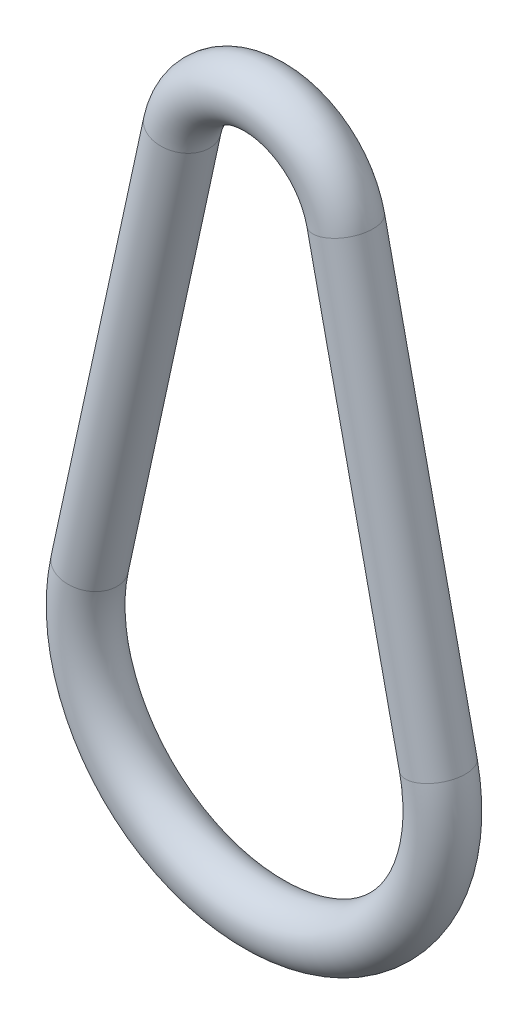
SolidWorks part; units mm, degrees
ref_plane "Front Plane" through (0, 0, 0) normal (0, 0, 1) x (1, 0, 0)
ref_plane "Top Plane" through (0, 0, 0) normal (0, 1, 0) x (1, 0, 0)
ref_plane "Right Plane" through (0, 0, 0) normal (1, 0, 0) x (0, 0, -1)
sketch "Sketch1" plane through (0, 0, 0) normal (0, 0, 1) x (1, 0, 0)
  line L0 (-14.6574, 83.1875) -> (-31.2692, 6.8)
  line L1 (0, 80) -> (0, 57.8431) construction
  line L2 (14.6574, 83.1875) -> (31.2692, 6.8)
  arc A0 (-31.2692, 6.8) -> (31.2692, 6.8) centre (0, 0) ccw
  arc A1 (14.6574, 83.1875) -> (-14.6574, 83.1875) centre (0, 80) ccw
  point P1 (0, 0)
  dimension "D1" = 30
  dimension "D2" = 64
  dimension "D3" = 80
ref_plane "Plane1" through (-31.2692, 6.8, 0) normal (-0.2125, -0.9772, 0) x (-0.9772, 0.2125, 0)
sketch "Sketch2" plane through (-31.2692, 6.8, 0) normal (-0.2125, -0.9772, 0) x (-0.9772, 0.2125, 0)
  circle A0 centre (0, 0) radius 5
  dimension "D1" = 10
sweep "Sweep1" add profiles "Sketch2" path "Sketch1"
